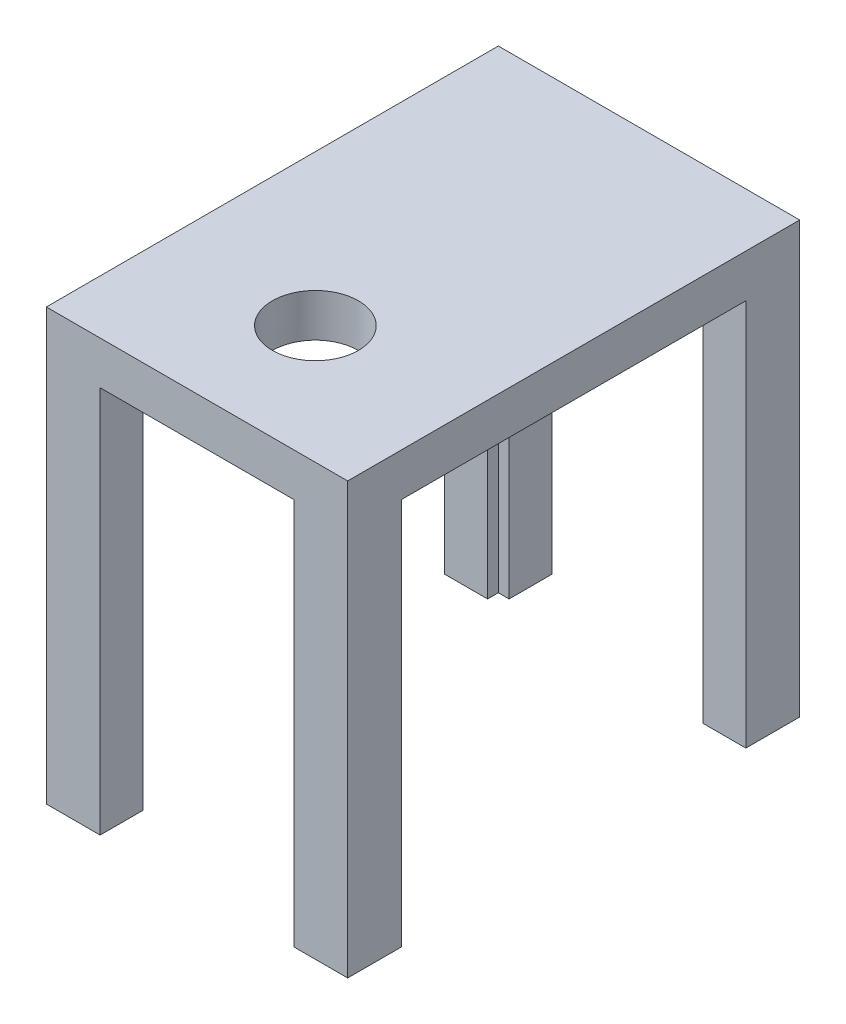
SolidWorks part; units mm, degrees
ref_plane "Front Plane" through (0, 0, 0) normal (0, 0, 1) x (1, 0, 0)
ref_plane "Top Plane" through (0, 0, 0) normal (0, 1, 0) x (1, 0, 0)
ref_plane "Right Plane" through (0, 0, 0) normal (1, 0, 0) x (0, 0, -1)
sketch "Sketch1" plane through (0, 0, 0) normal (0, 1, 0) x (1, 0, 0)
  line L1 (0, 0) -> (71.12, 0)
  line L2 (0, 0) -> (0, 106.68)
  line L3 (0, 106.68) -> (71.12, 106.68)
  line L4 (71.12, 0) -> (71.12, 106.68)
  dimension "D1" = 71.12
  dimension "D2" = 106.68
extrude "Boss-Extrude1" add sketch "Sketch1" along normal blind 101.6
shell "Shell1" thickness 10.16
sketch "Sketch3" plane through (0, 0, 0) normal (0, -1, 0) x (1, 0, 0)
  line L0 (0, 0) -> (71.12, 0) construction
  line L1 (0, -106.68) -> (0, 0) construction
  line L2 (6.35, -6.35) -> (6.35, -100.33) construction
  circle A0 centre (6.35, -6.35) radius 1.5875
  circle A1 centre (64.77, -6.35) radius 1.5875
  circle A2 centre (64.77, -100.33) radius 1.5875
  circle A3 centre (6.35, -100.33) radius 1.5875
  dimension "D1" = 6.35
  dimension "D2" = 6.35
  dimension "D5" = 93.98
  dimension "D3" = 2
  dimension "D4" = 2
extrude "Cut-Extrude1" cut sketch "Sketch3" against normal blind 10.16
sketch "Sketch4" plane through (0, 0, 0) normal (-1, 0, 0) x (0, 0, 1)
  line L0 (-106.68, 101.6) -> (0, 101.6) construction
  line L1 (-93.98, 0) -> (-12.7, 0)
  line L2 (-93.98, 0) -> (-93.98, 91.44)
  line L3 (-93.98, 91.44) -> (-12.7, 91.44)
  line L4 (-12.7, 0) -> (-12.7, 91.44)
  line L6 (0, 101.6) -> (0, 0) construction
  line L7 (-106.68, 101.6) -> (-106.68, 0) construction
  line L8 (-106.68, 0) -> (0, 0) construction
  dimension "D1" = 10.16
  dimension "D2" = 12.7
  dimension "D3" = 12.7
extrude "Cut-Extrude2" cut sketch "Sketch4" against normal through all
sketch "Sketch6" plane through (0, 0, 0) normal (0, -1, 0) x (1, 0, 0)
  line L0 (69.536, -6.35) -> (67.153, -2.2225)
  line L1 (11.116, -6.35) -> (8.733, -2.2225)
  line L2 (8.733, -2.2225) -> (3.967, -2.2225)
  line L3 (3.967, -2.2225) -> (1.584, -6.35)
  line L4 (1.584, -6.35) -> (3.967, -10.4775)
  line L5 (3.967, -10.4775) -> (8.733, -10.4775)
  line L6 (8.733, -10.4775) -> (11.116, -6.35)
  line L7 (67.153, -2.2225) -> (62.387, -2.2225)
  line L8 (62.387, -2.2225) -> (60.004, -6.35)
  line L9 (60.004, -6.35) -> (62.387, -10.4775)
  line L10 (62.387, -10.4775) -> (67.153, -10.4775)
  line L11 (67.153, -10.4775) -> (69.536, -6.35)
  line L12 (69.536, -100.33) -> (67.153, -96.2025)
  line L13 (67.153, -96.2025) -> (62.387, -96.2025)
  line L14 (62.387, -96.2025) -> (60.004, -100.33)
  line L15 (60.004, -100.33) -> (62.387, -104.4575)
  line L16 (62.387, -104.4575) -> (67.153, -104.4575)
  line L17 (67.153, -104.4575) -> (69.536, -100.33)
  line L18 (11.116, -100.33) -> (8.733, -96.2025)
  line L19 (8.733, -96.2025) -> (3.967, -96.2025)
  line L20 (3.967, -96.2025) -> (1.584, -100.33)
  line L21 (1.584, -100.33) -> (3.967, -104.4575)
  line L22 (3.967, -104.4575) -> (8.733, -104.4575)
  line L23 (8.733, -104.4575) -> (11.116, -100.33)
  circle A0 centre (6.35, -6.35) radius 4.1275 construction
  circle A1 centre (64.77, -6.35) radius 4.1275 construction
  circle A2 centre (64.77, -100.33) radius 4.1275 construction
  circle A3 centre (6.35, -100.33) radius 4.1275 construction
  dimension "D1" = 8.255
  dimension "D2" = 2
  dimension "D3" = 2
extrude "Cut-Extrude3" cut sketch "Sketch6" against normal blind 3.175
sketch "Sketch7" plane through (0, 0, -106.68) normal (0, 0, -1) x (-1, 0, 0)
  line L0 (-71.12, 101.6) -> (0, 101.6) construction
  line L1 (-58.42, 0) -> (-12.7, 0)
  line L2 (-58.42, 0) -> (-58.42, 91.44)
  line L3 (-58.42, 91.44) -> (-12.7, 91.44)
  line L4 (-12.7, 0) -> (-12.7, 91.44)
  line L6 (-71.12, 101.6) -> (-71.12, 0) construction
  line L7 (0, 101.6) -> (0, 0) construction
  dimension "D1" = 10.16
  dimension "D2" = 12.7
  dimension "D3" = 12.7
extrude "Cut-Extrude4" cut sketch "Sketch7" against normal through all and the other way through all
sketch "Sketch8" plane through (0, 101.6, 0) normal (0, 1, 0) x (1, 0, 0)
  line L0 (0, 0) -> (71.12, 0) construction
  circle A0 centre (35.56, 27.94) radius 10.16
  point P4 (35.56, 0)
  dimension "D1" = 20.32
  dimension "D2" = 27.94
extrude "Cut-Extrude5" cut sketch "Sketch8" against normal up to next
